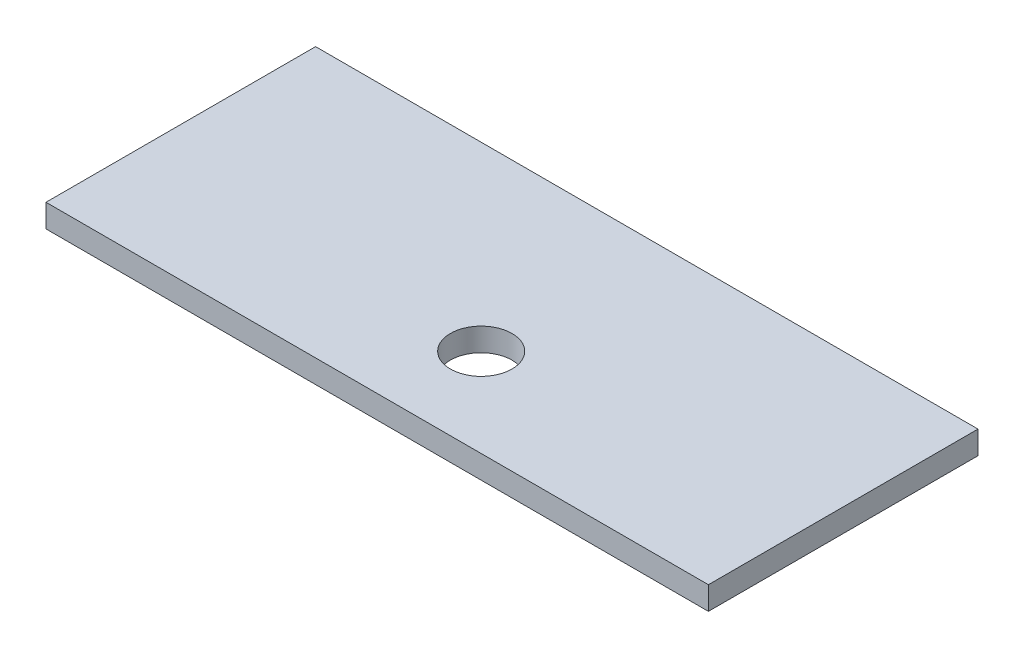
SolidWorks part; units mm, degrees
ref_plane "Спереди" through (0, 0, 0) normal (0, 0, 1) x (1, 0, 0)
ref_plane "Сверху" through (0, 0, 0) normal (0, 1, 0) x (1, 0, 0)
ref_plane "Справа" through (0, 0, 0) normal (1, 0, 0) x (0, 0, -1)
sketch "Эскиз1" plane through (0, 0, 0) normal (0, 1, 0) x (1, 0, 0)
  line L1 (0, 0) -> (43, 0)
  line L2 (0, 0) -> (0, 17.5)
  line L3 (0, 17.5) -> (43, 17.5)
  line L4 (43, 0) -> (43, 17.5)
  circle A1 centre (22.5, 5.75) radius 2
extrude "Бобышка-Вытянуть1" add sketch "Эскиз1" along normal blind 1.5
